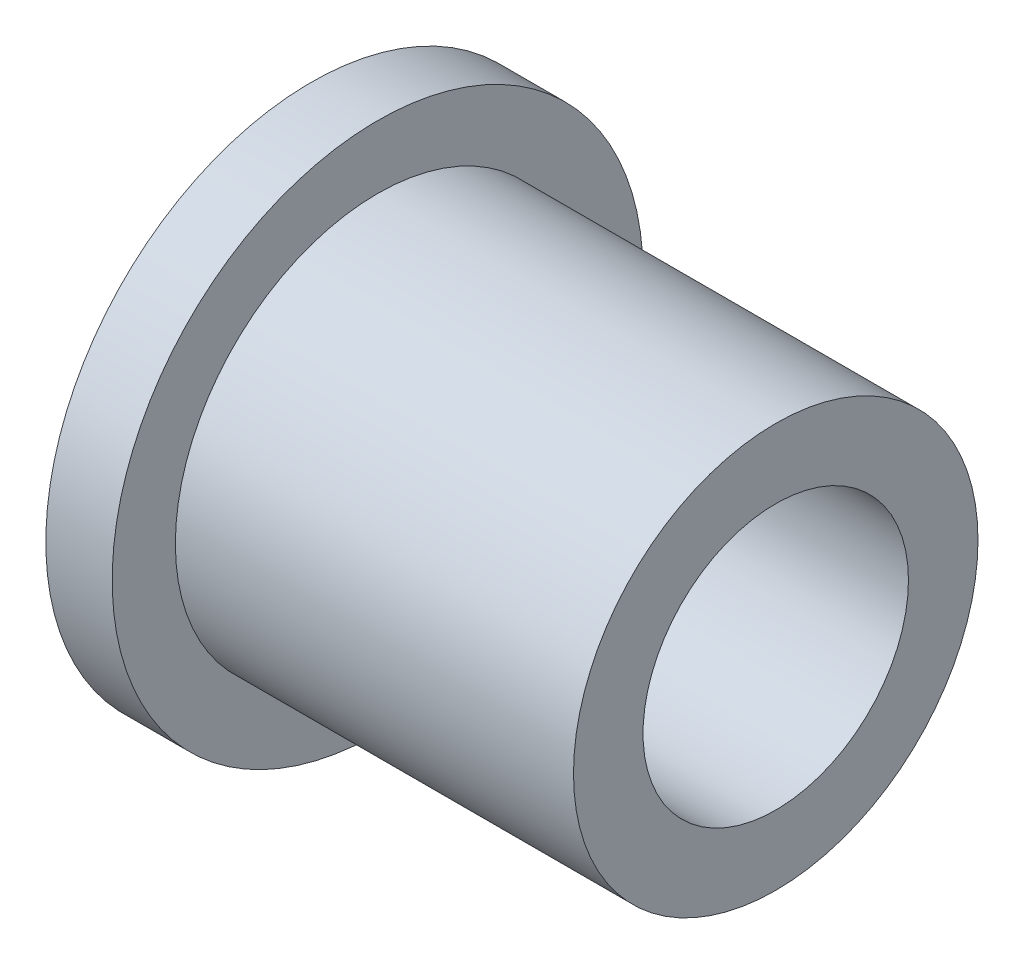
SolidWorks part; units mm, degrees
material "Brass"
ref_plane "Front Plane" through (0, 0, 0) normal (0, 0, 1) x (1, 0, 0)
ref_plane "Top Plane" through (0, 0, 0) normal (0, 1, 0) x (1, 0, 0)
ref_plane "Right Plane" through (0, 0, 0) normal (1, 0, 0) x (0, 0, -1)
sketch "Sketch1" plane through (0, 0, 0) normal (1, 0, 0) x (0, 0, -1)
  circle A0 centre (0, 0) radius 3.175
  circle A1 centre (0, 0) radius 6.35
  dimension "D1" = 6.35
  dimension "D2" = 12.7
extrude "Boss-Extrude1" add sketch "Sketch1" along normal blind 1.5875
sketch "Sketch2" plane through (1.5875, 0, 0) normal (1, 0, 0) x (0, 0, -1)
  circle A0 centre (0, 0) radius 3.175
  circle A1 centre (0, 0) radius 4.8387
  circle A2 centre (0, 0) radius 3.175 construction
  dimension "D1" = 9.6774
extrude "Boss-Extrude2" add sketch "Sketch2" along normal blind 9.525
